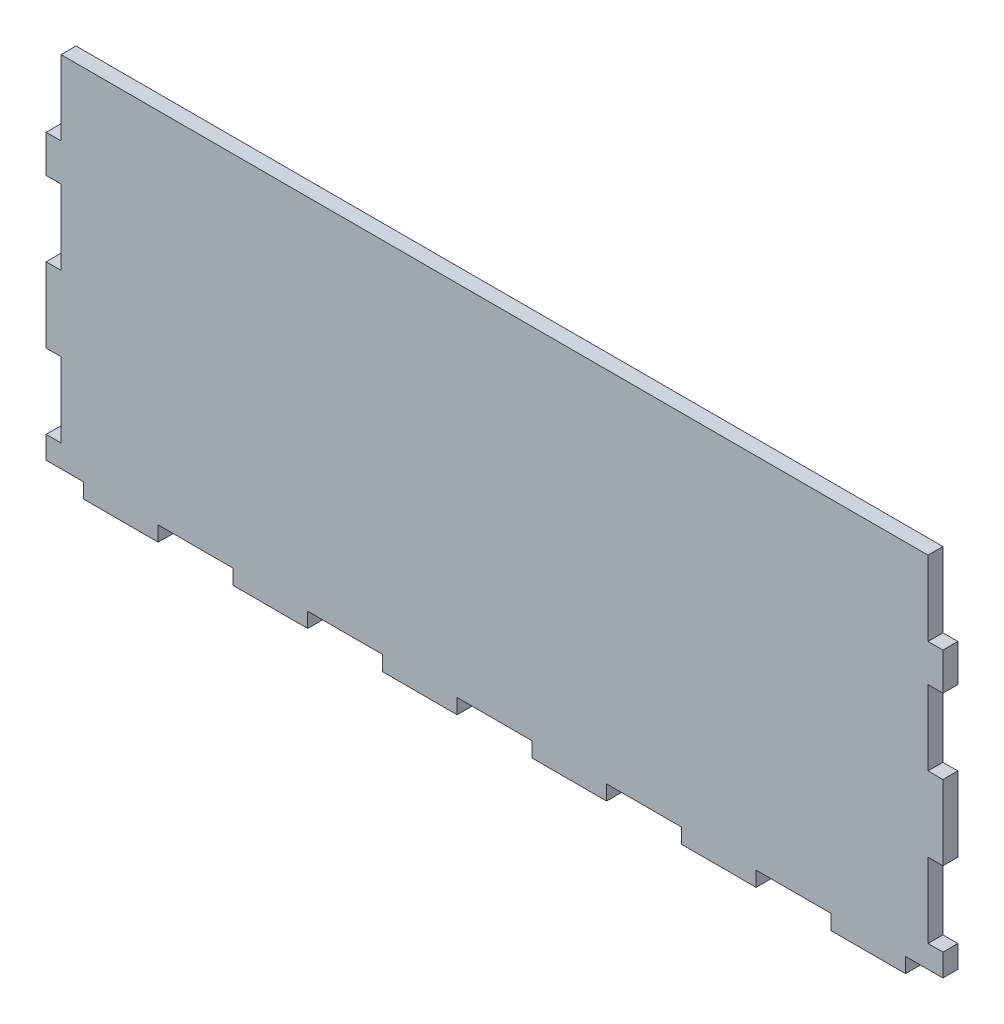
SolidWorks part; units mm, degrees
ref_plane "Front Plane" through (0, 0, 0) normal (0, 0, 1) x (1, 0, 0)
ref_plane "Top Plane" through (0, 0, 0) normal (0, 1, 0) x (1, 0, 0)
ref_plane "Right Plane" through (0, 0, 0) normal (1, 0, 0) x (0, 0, -1)
sketch "Sketch1" plane through (0, 0, 0) normal (0, 0, 1) x (1, 0, 0)
  line L0 (0, 0) -> (0, -127) construction
  line L1 (152.4, 0) -> (-152.4, 0)
  line L2 (12.7, -127) -> (-12.7, -127)
  line L3 (-12.7, -127) -> (-12.7, -121.92)
  line L4 (-12.7, -121.92) -> (-38.1, -121.92)
  line L5 (-38.1, -121.92) -> (-38.1, -127)
  line L6 (-38.1, -127) -> (-63.5, -127)
  line L7 (-63.5, -127) -> (-63.5, -121.92)
  line L8 (-63.5, -121.92) -> (-88.9, -121.92)
  line L9 (-88.9, -121.92) -> (-88.9, -127)
  line L10 (-88.9, -127) -> (-114.3, -127)
  line L11 (-152.4, -127) -> (-152.4, -114.3)
  line L12 (-114.3, -127) -> (-114.3, -121.92)
  line L13 (-114.3, -121.92) -> (-139.7, -121.92)
  line L14 (-139.7, -121.92) -> (-139.7, -127)
  line L15 (-139.7, -127) -> (-152.4, -127)
  line L16 (-152.4, -114.3) -> (-147.32, -114.3)
  line L17 (-147.32, -114.3) -> (-147.32, -88.9)
  line L18 (-147.32, -88.9) -> (-152.4, -88.9)
  line L19 (-152.4, -63.5) -> (-147.32, -63.5)
  line L20 (-147.32, -63.5) -> (-147.32, -38.1)
  line L21 (-147.32, -38.1) -> (-152.4, -38.1)
  line L22 (-152.4, -25.4) -> (-147.32, -25.4)
  line L23 (-147.32, -25.4) -> (-147.32, 0)
  line L24 (-152.4, -88.9) -> (-152.4, -63.5)
  line L25 (-152.4, -38.1) -> (-152.4, -25.4)
  line L26 (152.4, -38.1) -> (152.4, -25.4)
  line L27 (152.4, -88.9) -> (152.4, -63.5)
  line L28 (147.32, -25.4) -> (147.32, 0)
  line L29 (152.4, -25.4) -> (147.32, -25.4)
  line L30 (147.32, -38.1) -> (152.4, -38.1)
  line L31 (147.32, -63.5) -> (147.32, -38.1)
  line L32 (152.4, -63.5) -> (147.32, -63.5)
  line L33 (147.32, -88.9) -> (152.4, -88.9)
  line L34 (147.32, -114.3) -> (147.32, -88.9)
  line L35 (152.4, -114.3) -> (147.32, -114.3)
  line L36 (139.7, -127) -> (152.4, -127)
  line L37 (139.7, -121.92) -> (139.7, -127)
  line L38 (114.3, -121.92) -> (139.7, -121.92)
  line L39 (114.3, -127) -> (114.3, -121.92)
  line L40 (152.4, -127) -> (152.4, -114.3)
  line L41 (88.9, -127) -> (114.3, -127)
  line L42 (88.9, -121.92) -> (88.9, -127)
  line L43 (63.5, -121.92) -> (88.9, -121.92)
  line L44 (63.5, -127) -> (63.5, -121.92)
  line L45 (38.1, -127) -> (63.5, -127)
  line L46 (38.1, -121.92) -> (38.1, -127)
  line L47 (12.7, -121.92) -> (38.1, -121.92)
  line L48 (12.7, -127) -> (12.7, -121.92)
  line L49 (-147.32, 0) -> (147.32, 0)
  line L50 (-152.4, 0) -> (-152.4, -127)
  line L51 (-152.4, -127) -> (152.4, -127)
  line L52 (152.4, -127) -> (152.4, 0)
  line L53 (-147.32, 0) -> (-147.32, -114.3)
  line L54 (-139.7, -121.92) -> (139.7, -121.92)
  line L55 (147.32, 0) -> (147.32, -114.3)
  line L56 (-139.7, -121.92) -> (-152.4, -121.92)
  line L57 (139.7, -121.92) -> (152.4, -121.92)
  line L58 (-147.32, -114.3) -> (-147.32, -121.92)
  line L59 (147.32, -114.3) -> (147.32, -121.92)
  dimension "D1" = 152.4
  dimension "D2" = 127
  dimension "D3" = 12.7
  dimension "D4" = 25.4
  dimension "D5" = 5.08
  dimension "D6" = 12.7
  dimension "D7" = 25.4
extrude "Boss-Extrude1" add sketch "Sketch1" along normal mid plane 5.08 contours L53 L19 L24 L18 | L53 L22 L25 L21 | L58 L16 L50 L56 | L0 L49 L23 L53 L20 L17 L58 L56 L13 L54 L8 L4 | L14 L51 L12 L13 | L9 L51 L7 L8 | L5 L51 L3 L4 | L48 L51 L46 L47 | L1 L0 L54 L47 L43 L38 L57 L59 L34 L55 L31 L28 | L44 L51 L42 L43 | L39 L51 L37 L38 | L35 L59 L57 L52 | L32 L55 L33 L27 | L29 L55 L30 L26
